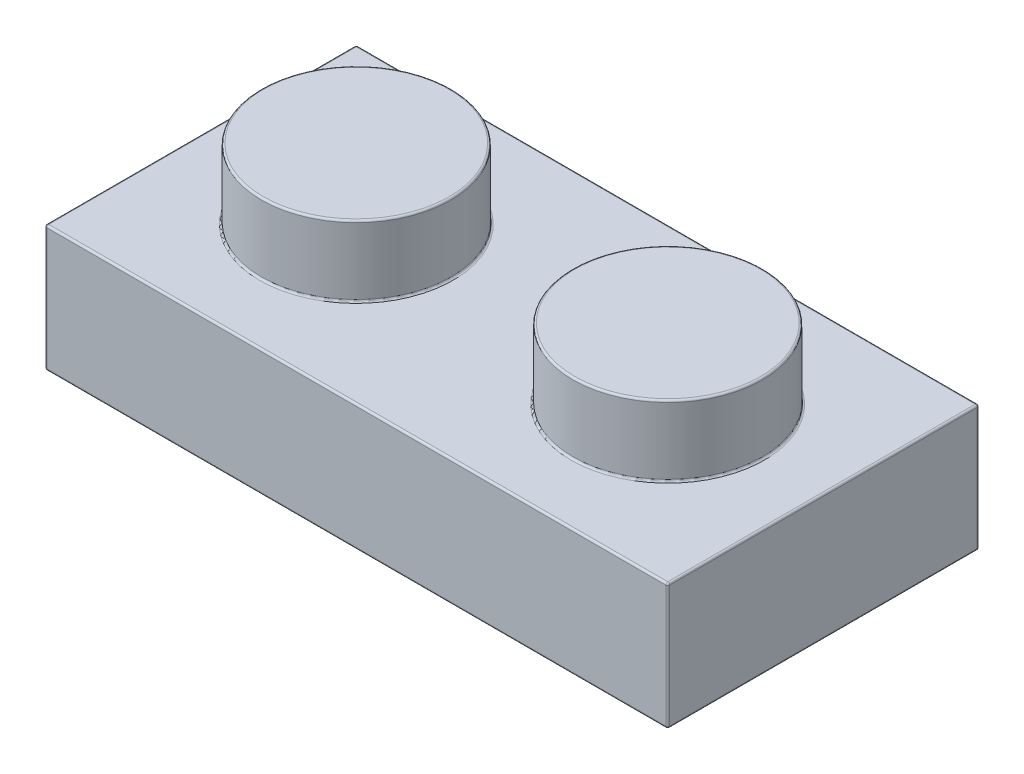
SolidWorks part; units mm, degrees
ref_plane "Front Plane" through (0, 0, 0) normal (0, 0, 1) x (1, 0, 0)
ref_plane "Top Plane" through (0, 0, 0) normal (0, 1, 0) x (1, 0, 0)
ref_plane "Right Plane" through (0, 0, 0) normal (1, 0, 0) x (0, 0, -1)
sketch "Sketch1" plane through (0, 0, 0) normal (0, 1, 0) x (1, 0, 0)
  line L1 (-3.98, 3.98) -> (3.98, 3.98)
  line L2 (-3.98, 3.98) -> (-3.98, -3.98)
  line L3 (-3.98, -3.98) -> (3.98, -3.98)
  line L4 (3.98, 3.98) -> (3.98, -3.98)
  line L5 (-3.98, 3.98) -> (3.98, -3.98) construction
  line L6 (-3.98, -3.98) -> (3.98, 3.98) construction
  point P0 (0, 0)
  dimension "D1" = 7.96
extrude "Extrude1" add sketch "Sketch1" along normal blind 3.22
sketch "Sketch2" plane through (0, 3.22, 0) normal (0, 1, 0) x (1, 0, 0)
  circle A0 centre (0, 0) radius 2.425
  dimension "D1" = 4.85
extrude "Extrude2" add sketch "Sketch2" along normal blind 1.8
pattern_linear "LPattern1" count 2 spacing 7.96 along (1, 0, 0) of "Extrude2", "Extrude1"
shell "Shell1" thickness 1.55
sketch "Sketch4" plane through (0, 1.67, 0) normal (0, -1, 0) x (1, 0, 0)
  line L0 (10.39, 2.43) -> (10.39, -2.43) construction
  line L1 (-2.43, 2.43) -> (10.39, 2.43) construction
  line L2 (-2.43, -2.43) -> (-2.43, 2.43) construction
  line L3 (10.39, -2.43) -> (-2.43, -2.43) construction
  line L4 (10.39, 2.43) -> (10.39, -2.43)
  line L5 (-2.43, 2.43) -> (10.39, 2.43)
  line L6 (-2.43, -2.43) -> (-2.43, 2.43)
  line L7 (10.39, -2.43) -> (-2.43, -2.43)
extrude "Extrude3" cut sketch "Sketch4" against normal blind 0.14
sketch "Sketch5" plane through (0, 1.81, 0) normal (0, -1, 0) x (1, 0, 0)
  line L0 (10.39, 2.43) -> (-2.43, 2.43) construction
  circle A0 centre (3.98, 0) radius 1.5
  circle A1 centre (3.98, 0) radius 0.64
  point P5 (3.98, 2.43)
  dimension "D1" = 3
  dimension "D2" = 0.86
extrude "Extrude4" add sketch "Sketch5" along normal up to surface (1.81 mm away) up to face at (3.98, 0, 0)
fillet "Fillet1" radius 0.05 36 edges at (3.98, 1.81, -0.64) (3.98, 0, 1.5) (3.98, 0, 0.64) (3.98, 1.81, 2.43) (-2.43, 1.81, 0) (3.98, 1.81, -2.43) (10.39, 1.81, 0) (7.96, 1.81, 0.875) (0, 1.81, 0.875) (7.96, 3.47, 0.875) (10.39, 0, 0) (10.39, 0.905, 2.43) (10.39, 0.905, -2.43) (0, 3.47, 0.875) (3.98, 0, -2.43) (-2.43, 0, 0) (3.98, 0, 2.43) (-2.43, 0.905, 2.43) (-2.43, 0.905, -2.43) (7.96, 3.22, 2.425) (7.96, 5.02, 2.425) (11.94, 0, 0) (11.94, 3.22, 0) (11.94, 1.61, -3.98) (11.94, 1.61, 3.98) (0, 3.22, 2.425) (0, 5.02, 2.425) (3.98, 0, -3.98) (-3.98, 0, 0) (3.98, 0, 3.98) (3.98, 3.22, -3.98) (-3.98, 3.22, 0) (3.98, 3.22, 3.98) (-3.98, 1.61, 3.98) (-3.98, 1.61, -3.98) (3.98, 1.81, 1.5)
